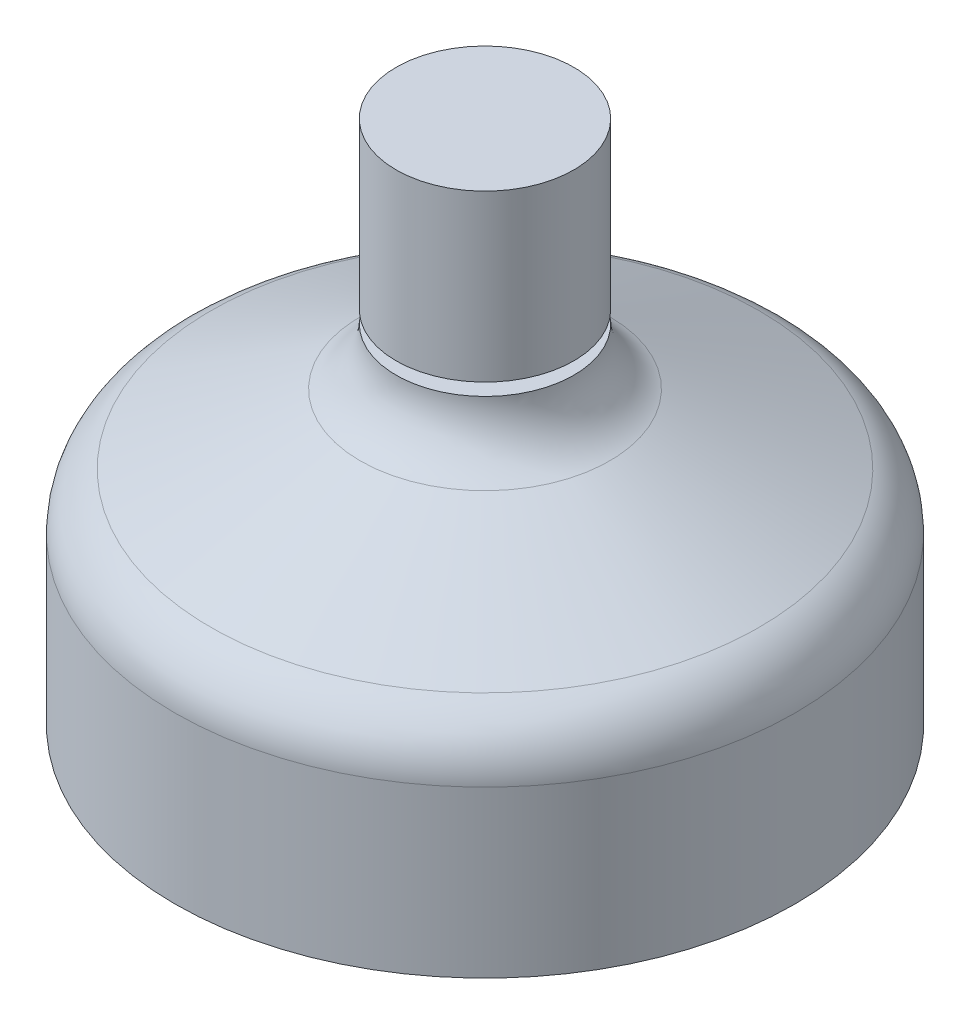
SolidWorks part; units mm, degrees
ref_plane "Front Plane" through (0, 0, 0) normal (0, 0, 1) x (1, 0, 0)
ref_plane "Top Plane" through (0, 0, 0) normal (0, 1, 0) x (1, 0, 0)
ref_plane "Right Plane" through (0, 0, 0) normal (1, 0, 0) x (0, 0, -1)
sketch "Sketch1" plane through (0, 0, 0) normal (0, 1, 0) x (1, 0, 0)
  circle A0 centre (0, 0) radius 3.75
  dimension "D1" = 7.5
ref_plane "Plane1" through (0, 6.35, 0) normal (0, 1, 0) x (1, 0, 0)
sketch "Sketch2" plane through (0, 6.35, 0) normal (0, 1, 0) x (1, 0, 0)
  circle A0 centre (0, 0) radius 1.075
  dimension "D1" = 2.15
sketch "Sketch6" plane through (0, 0, 0) normal (1, 0, 0) x (0, 0, -1)
  line L0 (-3.75, 0) -> (-3.75, 2)
  line L1 (-3.316, 2.6802) -> (-1.509, 3.5198)
  arc A0 (-1.075, 4.2) -> (-1.509, 3.5198) centre (-1.825, 4.2) cw
  arc A1 (-3.75, 2) -> (-3.316, 2.6802) centre (-3, 2) cw
  dimension "D2" = 2
sketch "Sketch7" plane through (0, 0, 0) normal (1, 0, 0) x (0, 0, -1)
  line L0 (0, -0.2276) -> (0, 2.526)
revolve "Revolve-Thin2" add sketch "Sketch6" angle 360 about L0
extrude "Boss-Extrude2" add sketch "Sketch2" against normal blind 2
